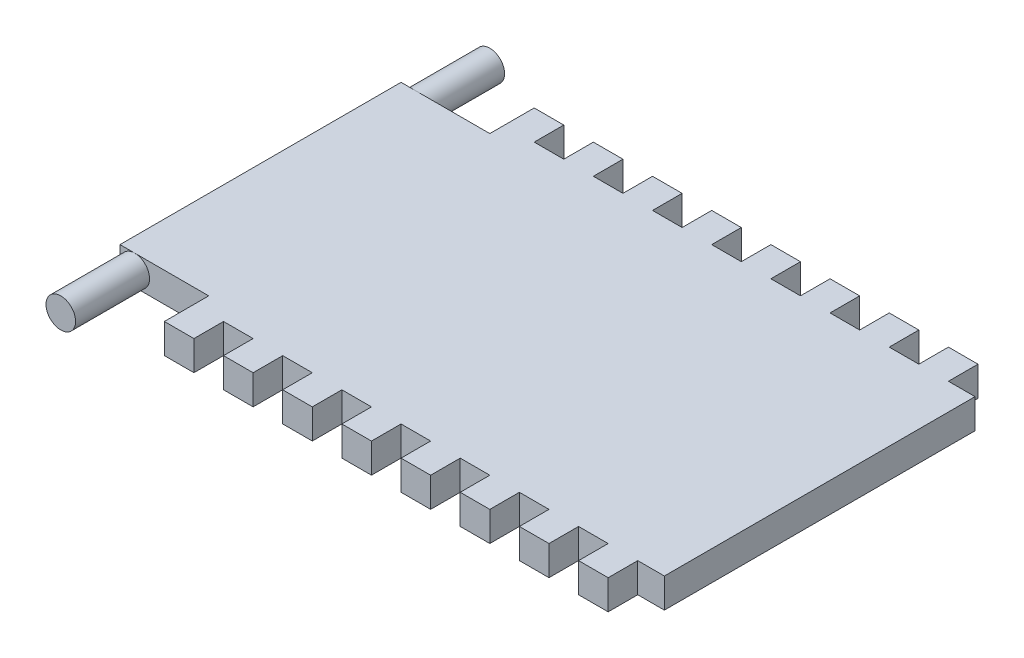
SolidWorks part; units mm, degrees
ref_plane "Plan de face" through (0, 0, 0) normal (0, 0, 1) x (1, 0, 0)
ref_plane "Plan de dessus" through (0, 0, 0) normal (0, 1, 0) x (1, 0, 0)
ref_plane "Plan de droite" through (0, 0, 0) normal (1, 0, 0) x (0, 0, -1)
sketch "Esquisse1" plane through (0, 0, 0) normal (0, 1, 0) x (1, 0, 0)
  line L1 (0, 0) -> (-189, 0)
  line L2 (0, 0) -> (0, 125)
  line L3 (0, 125) -> (-189, 125)
  line L4 (-189, 0) -> (-189, 125)
  dimension "D1" = 189
  dimension "D2" = 125
extrude "Boss.-Extru.1" add sketch "Esquisse1" along normal blind 10
sketch "Esquisse2" plane through (0, 10, 0) normal (0, 1, 0) x (1, 0, 0)
  line L1 (-189, 125) -> (-159, 125)
  line L2 (-189, 125) -> (-189, 110)
  line L3 (-189, 110) -> (-159, 110)
  line L4 (-159, 125) -> (-159, 110)
  line L5 (-189, 0) -> (-159, 0)
  line L6 (-189, 0) -> (-189, 15)
  line L7 (-189, 15) -> (-159, 15)
  line L8 (-159, 0) -> (-159, 15)
  dimension "D1" = 15
  dimension "D2" = 15
  dimension "D3" = 30
  dimension "D4" = 30
extrude "Enlèv. mat.-Extru.1" cut sketch "Esquisse2" against normal blind 10
sketch "Esquisse3" plane through (0, 10, 0) normal (0, 1, 0) x (1, 0, 0)
  line L0 (0, 125) -> (-159, 125) construction
  line L1 (-149, 125) -> (-139, 125)
  line L2 (-149, 125) -> (-149, 115)
  line L3 (-149, 115) -> (-139, 115)
  line L4 (-139, 125) -> (-139, 115)
  line L5 (-159, 110) -> (-159, 125) construction
  line L6 (-159, 0) -> (0, 0) construction
  line L7 (-149, 0) -> (-139, 0)
  line L8 (-149, 0) -> (-149, 10)
  line L9 (-149, 10) -> (-139, 10)
  line L10 (-139, 0) -> (-139, 10)
  line L11 (-159, 0) -> (-159, 15) construction
  dimension "D1" = 10
  dimension "D2" = 10
  dimension "D3" = 10
  dimension "D4" = 10
  dimension "D5" = 10
  dimension "D6" = 10
extrude "Enlèv. mat.-Extru.2" cut sketch "Esquisse3" against normal blind 10
pattern_linear "Répétition linéaire1" count 8 spacing 20 along (1, 0, 0) of "Enlèv. mat.-Extru.2"
sketch "Esquisse4" plane through (0, 0, -15) normal (0, 0, 1) x (1, 0, 0)
  line L0 (-159, 10) -> (-189, 10) construction
  line L1 (-189, 0) -> (-189, 10) construction
  line L2 (-159, 0) -> (-189, 0) construction
  circle A0 centre (-184, 5) radius 5
extrude "Boss.-Extru.2" add sketch "Esquisse4" along normal blind 25
sketch "Esquisse5" plane through (0, 0, -110) normal (0, 0, -1) x (-1, 0, 0)
  line L0 (189, 0) -> (159, 0) construction
  line L1 (189, 10) -> (159, 10) construction
  line L2 (189, 0) -> (189, 10) construction
  circle A0 centre (184, 5) radius 5
extrude "Boss.-Extru.4" add sketch "Esquisse5" along normal blind 25
